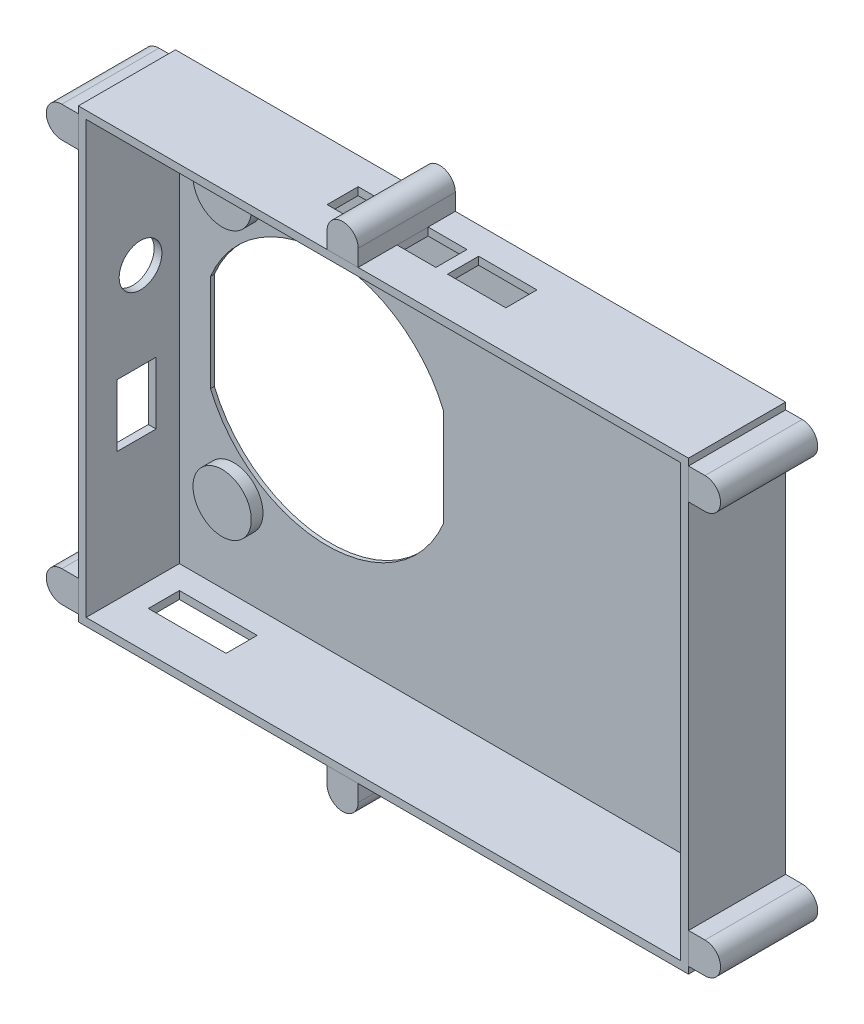
SolidWorks part; units mm, degrees
ref_plane "Front Plane" through (0, 0, 0) normal (0, 0, 1) x (1, 0, 0)
ref_plane "Top Plane" through (0, 0, 0) normal (0, 1, 0) x (1, 0, 0)
ref_plane "Right Plane" through (0, 0, 0) normal (1, 0, 0) x (0, 0, -1)
sketch "Sketch1" plane through (0, 0, 0) normal (0, 0, 1) x (1, 0, 0)
  line L1 (-78.5, 57.5) -> (78.5, 57.5)
  line L2 (-78.5, 57.5) -> (-78.5, -57.5)
  line L3 (-78.5, -57.5) -> (78.5, -57.5)
  line L4 (78.5, 57.5) -> (78.5, -57.5)
  line L5 (-78.5, 57.5) -> (78.5, -57.5) construction
  line L6 (-78.5, -57.5) -> (78.5, 57.5) construction
  point P0 (0, 0)
  dimension "D1" = 157
  dimension "D2" = 115
extrude "Boss-Extrude1" add sketch "Sketch1" along normal blind 1
sketch "Sketch2" plane through (0, 0, 1) normal (0, 0, 1) x (1, 0, 0)
  line L0 (78.5, -57.5) -> (78.5, 57.5) construction
  line L1 (-78.5, 57.5) -> (78.5, 57.5)
  line L2 (-78.5, 57.5) -> (-78.5, 55.5)
  line L3 (-78.5, 55.5) -> (78.5, 55.5)
  line L4 (78.5, 57.5) -> (78.5, 55.5)
  line L6 (-78.5, -57.5) -> (78.5, -57.5)
  line L7 (-78.5, -57.5) -> (-78.5, -55.5)
  line L8 (-78.5, -55.5) -> (78.5, -55.5)
  line L9 (78.5, -57.5) -> (78.5, -55.5)
  line L10 (-78.5, -55.5) -> (-76.5, -55.5)
  line L11 (-78.5, -55.5) -> (-78.5, 55.5)
  line L12 (-78.5, 55.5) -> (-76.5, 55.5)
  line L13 (-76.5, -55.5) -> (-76.5, 55.5)
  line L14 (78.5, -55.5) -> (76.5, -55.5)
  line L15 (78.5, -55.5) -> (78.5, 55.5)
  line L16 (78.5, 55.5) -> (76.5, 55.5)
  line L17 (76.5, -55.5) -> (76.5, 55.5)
  line M7 (78.5, -57.5) -> (78.5, 57.5)
  line M8 (78.5, 57.5) -> (-78.5, 57.5)
  line M9 (-78.5, 57.5) -> (-78.5, -57.5)
  line M10 (-78.5, -57.5) -> (78.5, -57.5)
  dimension "D1" = 2
  dimension "D2" = 2
  dimension "D3" = 2
  dimension "D4" = 2
extrude "Boss-Extrude2" add sketch "Sketch2" along normal blind 24 contours L8 L13 L3 M9 | L3 M9 M7 M8 | L17 L8 L3 M7 | L8 M9 M10 M7
sketch "Sketch4" plane through (-78.5, 0, 0) normal (-1, 0, 0) x (0, 0, 1)
  line L0 (25, -57.5) -> (0, -57.5) construction
  line L1 (17, -6.5) -> (7, -6.5)
  line L2 (17, -6.5) -> (17, -22.5)
  line L3 (17, -22.5) -> (7, -22.5)
  line L4 (7, -6.5) -> (7, -22.5)
  line L5 (25, 57.5) -> (0, 57.5) construction
  line L6 (0, 57.5) -> (0, -57.5) construction
  circle A0 centre (11, 16) radius 5.5
  dimension "D5" = 11
  dimension "D6" = 11
  dimension "D7" = 41.5
  dimension "D1" = 16
  dimension "D2" = 10
  dimension "D3" = 35
  dimension "D4" = 17
extrude "Cut-Extrude1" cut sketch "Sketch4" against normal up to next
sketch "Sketch5" plane through (0, -57.5, 0) normal (0, -1, 0) x (1, 0, 0)
  line L0 (-78.5, 0) -> (78.5, 0) construction
  line L1 (-70.5, 15) -> (-50.5, 15)
  line L2 (-70.5, 15) -> (-70.5, 7)
  line L3 (-70.5, 7) -> (-50.5, 7)
  line L4 (-50.5, 15) -> (-50.5, 7)
  line L6 (-78.5, 25) -> (-78.5, 0) construction
  dimension "D1" = 20
  dimension "D2" = 8
  dimension "D3" = 7
  dimension "D4" = 8
extrude "Cut-Extrude2" cut sketch "Sketch5" against normal up to next
sketch "Sketch6" plane through (0, 57.5, 0) normal (0, 1, 0) x (1, 0, 0)
  line L0 (-78.5, -25) -> (-78.5, 0) construction
  line L1 (-14.5, -15) -> (-24.5, -15)
  line L2 (-14.5, -15) -> (-14.5, -7)
  line L3 (-14.5, -7) -> (-24.5, -7)
  line L4 (-24.5, -15) -> (-24.5, -7)
  line L5 (78.5, 0) -> (-78.5, 0) construction
  line L7 (3.5, -15) -> (-6.5, -15)
  line L8 (3.5, -15) -> (3.5, -7)
  line L9 (3.5, -7) -> (-6.5, -7)
  line L10 (-6.5, -15) -> (-6.5, -7)
  line L11 (21.5, -15) -> (6.5, -15)
  line L12 (21.5, -15) -> (21.5, -7)
  line L13 (21.5, -7) -> (6.5, -7)
  line L14 (6.5, -15) -> (6.5, -7)
  dimension "D1" = 10
  dimension "D2" = 64
  dimension "D3" = 7
  dimension "D4" = 8
  dimension "D5" = 10
  dimension "D6" = 8
  dimension "D7" = 7
  dimension "D8" = 82
  dimension "D9" = 8
  dimension "D10" = 7
  dimension "D11" = 15
  dimension "D12" = 100
extrude "Cut-Extrude3" cut sketch "Sketch6" against normal up to next
sketch "Sketch7" plane through (0, 0, 0) normal (0, 0, -1) x (-1, 0, 0)
  line L0 (78.5, 57.5) -> (78.5, -57.5) construction
  line L1 (-78.5, 57.5) -> (78.5, 57.5) construction
  line L2 (78.5, -57.5) -> (-78.5, -57.5) construction
  line L3 (-78.5, -57.5) -> (-78.5, 57.5) construction
  circle A0 centre (-64.5, 35.5) radius 0.5
  circle A1 centre (-64.5, -38.5) radius 0.5
  circle A2 centre (62.5, -33.5) radius 0.5
  circle A3 centre (62.5, 35.5) radius 0.5
  dimension "D1" = 1
  dimension "D2" = 16
  dimension "D3" = 22
  dimension "D4" = 1
  dimension "D5" = 24
  dimension "D6" = 16
  dimension "D7" = 1
  dimension "D8" = 14
  dimension "D9" = 19
  dimension "D10" = 1
  dimension "D11" = 14
  dimension "D12" = 22
  dimension "D13" = 74
sketch "Sketch8" plane through (0, 0, 0) normal (0, 0, -1) x (-1, 0, 0)
  circle A0 centre (-64.5, 35.5) radius 7.5
  circle A1 centre (62.5, 35.5) radius 7.5
  circle A2 centre (62.5, -33.5) radius 7.5
  circle A3 centre (-64.5, -38.5) radius 7.5
  dimension "D1" = 15
  dimension "D2" = 15
  dimension "D3" = 15
  dimension "D4" = 15
extrude "Boss-Extrude3" add sketch "Sketch8" against normal blind 4
sketch "Sketch9" plane through (0, 0, 0) normal (0, 0, -1) x (-1, 0, 0)
  line L1 (8.5, -32.5) -> (68.5, -32.5)
  line L2 (8.5, -32.5) -> (8.5, 32.5)
  line L3 (8.5, 32.5) -> (68.5, 32.5)
  line L4 (68.5, -32.5) -> (68.5, 32.5)
  line L5 (78.5, -57.5) -> (-78.5, -57.5) construction
  line L6 (8.5, -32.5) -> (68.5, 32.5)
  line L7 (68.5, -32.5) -> (8.5, 32.5)
  line L12 (78.5, 57.5) -> (78.5, -57.5) construction
  circle A0 centre (38.5, 0) radius 32.5
  dimension "D1" = 60
  dimension "D2" = 70
  dimension "D3" = 90
  dimension "D4" = 65
extrude "Cut-Extrude5" cut sketch "Sketch9" against normal up to next contours L7 A0 L6 | L6 A0 L7 | A0 L6 L7 | L6 A0 L7
sketch "Sketch13" plane through (0, 0, 0) normal (0, 0, -1) x (-1, 0, 0)
  line L0 (-78.5, 57.5) -> (78.5, 57.5) construction
  line L2 (-78.5, -57.5) -> (-78.5, 57.5) construction
  line L3 (-78.5, -55.75) -> (-82.75, -55.75)
  line L4 (-78.5, -55.75) -> (-78.5, -47.75)
  line L5 (78.5, 57.5) -> (78.5, -57.5) construction
  line L6 (-78.5, -47.75) -> (-82.75, -47.75)
  line L8 (-78.5, 55.75) -> (-82.75, 55.75)
  line L9 (78.5, -55.75) -> (82.75, -55.75)
  line L10 (78.5, -55.75) -> (78.5, -47.75)
  line L11 (78.5, -47.75) -> (82.75, -47.75)
  line L12 (82.75, -55.75) -> (82.75, -47.75)
  line L13 (78.5, 55.75) -> (82.75, 55.75)
  line L14 (78.5, 55.75) -> (78.5, 47.75)
  line L15 (78.5, 47.75) -> (82.75, 47.75)
  line L16 (82.75, 55.75) -> (82.75, 47.75)
  line L17 (14.5, 57.5) -> (6.5, 57.5)
  line L18 (14.5, 57.5) -> (14.5, 61.75)
  line L19 (14.5, 61.75) -> (6.5, 61.75)
  line L20 (6.5, 57.5) -> (6.5, 61.75)
  line L21 (78.5, -57.5) -> (-78.5, -57.5) construction
  line L22 (14.5, -57.5) -> (6.5, -57.5)
  line L23 (14.5, -57.5) -> (14.5, -61.75)
  line L24 (14.5, -61.75) -> (6.5, -61.75)
  line L25 (6.5, -57.5) -> (6.5, -61.75)
  line L26 (-82.75, -55.75) -> (-82.75, -47.75)
  line L27 (-78.5, 55.75) -> (-78.5, 47.75)
  line L28 (-78.5, 47.75) -> (-82.75, 47.75)
  line L29 (-82.75, 55.75) -> (-82.75, 47.75)
  circle A0 centre (-82.75, -51.75) radius 4
  circle A1 centre (-82.75, 51.75) radius 4
  circle A4 centre (82.75, -51.75) radius 4
  circle A6 centre (82.75, 51.75) radius 4
  circle A8 centre (10.5, 61.75) radius 4
  circle A10 centre (10.5, -61.75) radius 4
  dimension "D3" = 1.75
  dimension "D6" = 1.75
  dimension "D22" = 8
  dimension "D10" = 1.75
  dimension "D4" = 4.25
  dimension "D5" = 8
  dimension "D7" = 4.25
  dimension "D8" = 8
  dimension "D9" = 4.25
  dimension "D13" = 8
  dimension "D14" = 4.25
  dimension "D16" = 64
  dimension "D17" = 4.25
  dimension "D19" = 4.25
  dimension "D20" = 8
  dimension "D21" = 8
  dimension "D23" = 64
  dimension "D24" = 1.75
extrude "Boss-Extrude5" add sketch "Sketch13" against normal up to surface (25 mm away) separate body
